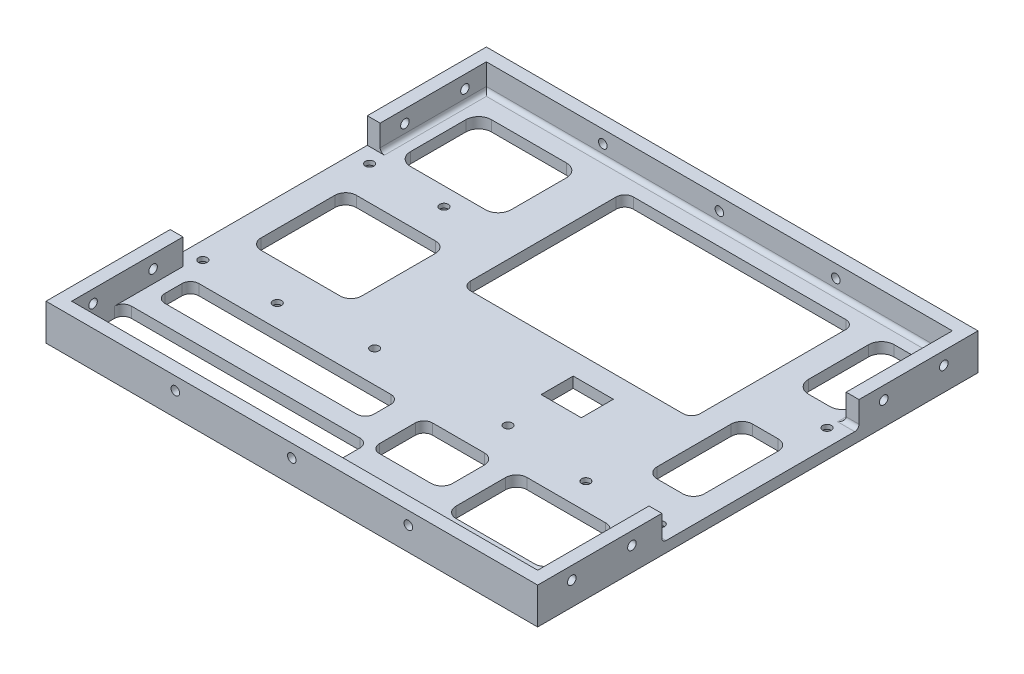
SolidWorks part; units mm, degrees
material "Custom Plastic"
ref_plane "Front Plane" through (0, 0, 0) normal (0, 0, 1) x (1, 0, 0)
ref_plane "Top Plane" through (0, 0, 0) normal (0, 1, 0) x (1, 0, 0)
ref_plane "Right Plane" through (0, 0, 0) normal (1, 0, 0) x (0, 0, -1)
sketch "Sketch1" plane through (0, 0, 0) normal (0, 1, 0) x (1, 0, 0)
  line L1 (-59.5, -51.5) -> (59.5, -51.5)
  line L2 (-59.5, -51.5) -> (-59.5, 51.5)
  line L3 (-59.5, 51.5) -> (59.5, 51.5)
  line L4 (59.5, -51.5) -> (59.5, 51.5)
  line L5 (-59.5, -51.5) -> (59.5, 51.5) construction
  line L6 (-59.5, 51.5) -> (59.5, -51.5) construction
  point P0 (0, 0)
  dimension "D1" = 119
  dimension "D2" = 103
extrude "Boss-Extrude1" add sketch "Sketch1" along normal blind 2.5
sketch "Sketch3" plane through (0, 2.5, 0) normal (0, 1, 0) x (1, 0, 0)
  line L0 (-59.5, -51.5) -> (59.5, -51.5) construction
  line L1 (-18.5, -5.5) -> (36.5, -5.5)
  line L2 (-18.5, -5.5) -> (-18.5, 38.5)
  line L3 (-18.5, 38.5) -> (36.5, 38.5)
  line L4 (36.5, -5.5) -> (36.5, 38.5)
  line L5 (-18.5, -5.5) -> (36.5, 38.5) construction
  line L6 (-18.5, 38.5) -> (36.5, -5.5) construction
  line L7 (-59.5, 51.5) -> (-59.5, -51.5) construction
  point P0 (9, 16.5)
  dimension "D1" = 46
  dimension "D2" = 41
  dimension "D3" = 44
  dimension "D4" = 55
extrude "Cut-Extrude2" cut sketch "Sketch3" against normal blind 10
sketch "Sketch4" plane through (-59.5, 0, 0) normal (-1, 0, 0) x (0, 0, 1)
  line L4 (-51.5, 0) -> (51.5, 0)
  line L5 (51.5, 0) -> (51.5, 2.5)
  line L6 (51.5, 2.5) -> (-51.5, 2.5)
  line L7 (-51.5, 2.5) -> (-51.5, 0)
  line L8 (-51.5, 0) -> (51.5, 0)
  line L9 (51.5, 0) -> (51.5, 2.5)
  line L10 (51.5, 2.5) -> (-51.5, 2.5)
  line L11 (-51.5, 2.5) -> (-51.5, 0)
  dimension "D1" = 0
extrude "Boss-Extrude2" add sketch "Sketch4" along normal blind 1.5
sketch "Sketch5" plane through (59.5, 0, 0) normal (1, 0, 0) x (0, 0, -1)
  line L4 (-51.5, 0) -> (51.5, 0)
  line L5 (51.5, 0) -> (51.5, 2.5)
  line L6 (51.5, 2.5) -> (-51.5, 2.5)
  line L7 (-51.5, 2.5) -> (-51.5, 0)
  line L8 (-51.5, 0) -> (51.5, 0)
  line L9 (51.5, 0) -> (51.5, 2.5)
  line L10 (51.5, 2.5) -> (-51.5, 2.5)
  line L11 (-51.5, 2.5) -> (-51.5, 0)
  dimension "D1" = 0
extrude "Boss-Extrude3" add sketch "Sketch5" along normal blind 1.5
sketch "Sketch6" plane through (-61, 0, 0) normal (-1, 0, 0) x (0, 0, 1)
  line L4 (-51.5, 2.5) -> (-51.5, 0)
  line L5 (-51.5, 0) -> (51.5, 0)
  line L6 (51.5, 0) -> (51.5, 2.5)
  line L7 (51.5, 2.5) -> (-51.5, 2.5)
  line L8 (-51.5, 2.5) -> (-51.5, 0)
  line L9 (-51.5, 0) -> (51.5, 0)
  line L10 (51.5, 0) -> (51.5, 2.5)
  line L11 (51.5, 2.5) -> (-51.5, 2.5)
  dimension "D1" = 0
extrude "Cut-Extrude3" cut sketch "Sketch6" against normal blind 3.5
sketch "Sketch7" plane through (61, 0, 0) normal (1, 0, 0) x (0, 0, -1)
  line L4 (-51.5, 2.5) -> (-51.5, 0)
  line L5 (-51.5, 0) -> (51.5, 0)
  line L6 (51.5, 0) -> (51.5, 2.5)
  line L7 (51.5, 2.5) -> (-51.5, 2.5)
  line L8 (-51.5, 2.5) -> (-51.5, 0)
  line L9 (-51.5, 0) -> (51.5, 0)
  line L10 (51.5, 0) -> (51.5, 2.5)
  line L11 (51.5, 2.5) -> (-51.5, 2.5)
  dimension "D1" = 0
extrude "Cut-Extrude4" cut sketch "Sketch7" against normal blind 3.5
sketch "Sketch8" plane through (0, 2.5, 0) normal (0, 1, 0) x (1, 0, 0)
  line L0 (-57.5, -51.5) -> (-57.5, 51.5) construction
  line L1 (-57.5, -51.5) -> (57.5, -51.5) construction
  line L3 (0, 59.9293) -> (0, -77.2132) construction
  circle A0 centre (-15.5, -44.96) radius 1
  circle A1 centre (15.7, -44.96) radius 1
  circle A2 centre (-15.5, -16.63) radius 1
  circle A3 centre (15.7, -16.63) radius 1
  circle A4 centre (-53.5, -18.81) radius 1
  circle A5 centre (-36.1, -18.81) radius 1
  circle A6 centre (-53.5, 20.19) radius 1
  circle A7 centre (-36.1, 20.19) radius 1
  circle A8 centre (36.1, -18.81) radius 1
  circle A9 centre (53.5, -18.81) radius 1
  circle A10 centre (53.5, 20.19) radius 1
  dimension "D1" = 2
  dimension "D2" = 2
  dimension "D7" = 2
  dimension "D8" = 2
  dimension "D13" = 2
  dimension "D14" = 2
  dimension "D15" = 2
  dimension "D16" = 2
  dimension "D3" = 42
  dimension "D4" = 31.2
  dimension "D5" = 6.54
  dimension "D6" = 6.54
  dimension "D9" = 28.33
  dimension "D10" = 28.33
  dimension "D11" = 32.69
  dimension "D12" = 4
  dimension "D17" = 4
  dimension "D18" = 39
  dimension "D19" = 17.4
extrude "Cut-Extrude5" cut sketch "Sketch8" against normal blind 10
sketch "Sketch12" plane through (0, 2.5, 0) normal (0, 1, 0) x (1, 0, 0)
  line L0 (18.4571, -37.3668) -> (6.3413, -37.3668)
  line L1 (-48.6757, -10.0359) -> (-30.1363, -10.0359)
  line L2 (-51.1757, -7.5359) -> (-51.1757, 9.7595)
  line L3 (-48.6757, 12.2595) -> (-30.1363, 12.2595)
  line L4 (-27.6363, -7.5359) -> (-27.6363, 9.7595)
  line L5 (-51.1757, -10.0359) -> (-27.6363, 12.2595) construction
  line L6 (-51.1757, 12.2595) -> (-27.6363, -10.0359) construction
  line L7 (4.3413, -35.3668) -> (4.3413, -26.9455)
  line L8 (6.3413, -24.9455) -> (18.4571, -24.9455)
  line L9 (-57.5, -51.5) -> (57.5, -51.5) construction
  line L10 (0.9414, -48.5) -> (-52.5, -48.5)
  line L11 (2.9414, -46.5) -> (2.9414, -38.5)
  line L12 (20.9571, -34.8668) -> (20.9571, -27.4455)
  line L13 (0.9414, -36.5) -> (-52.5, -36.5)
  line L14 (28.4571, -41.5653) -> (46.8503, -41.5653)
  line L15 (49.3503, -39.0653) -> (49.3503, -27.4455)
  line L16 (46.8503, -24.9455) -> (28.4571, -24.9455)
  line L17 (25.9571, -27.4455) -> (25.9571, -39.0653)
  line L18 (0, 20.449) -> (0, -71.2445) construction
  line L19 (41.5, 9.7595) -> (41.5, -7.5359)
  line L20 (44, -10.0359) -> (50, -10.0359)
  line L21 (52.5, -7.5359) -> (52.5, 9.7595)
  line L22 (50, 12.2595) -> (44, 12.2595)
  line L23 (57.5, 51.5) -> (57.5, -51.5) construction
  line L24 (36.5, -5.5) -> (36.5, 38.5) construction
  line L25 (-54.5, -46.5) -> (-54.5, -38.5)
  line L26 (-57.5, -51.5) -> (-57.5, 51.5) construction
  line L28 (-4.2775, -32.0334) -> (-49.1757, -32.0334)
  line L29 (-2.2775, -30.0334) -> (-2.2775, -26.0334)
  line L30 (-4.2775, -24.0334) -> (-49.1757, -24.0334)
  line L31 (-51.1757, -30.0334) -> (-51.1757, -26.0334)
  line L32 (-30.6363, 24.426) -> (-48.1757, 24.426)
  line L33 (-27.6363, 27.426) -> (-27.6363, 40.3779)
  line L34 (-30.6363, 43.3779) -> (-48.1757, 43.3779)
  line L35 (-51.1757, 27.426) -> (-51.1757, 40.3779)
  line L36 (49.5, 24.8453) -> (44.5, 24.8453)
  line L37 (52.5, 27.8453) -> (52.5, 41.8947)
  line L38 (49.5, 44.8947) -> (44.5, 44.8947)
  line L39 (41.5, 27.8453) -> (41.5, 41.8947)
  arc A0 (52.5, 9.7595) -> (50, 12.2595) centre (50, 9.7595) ccw
  arc A1 (50, -10.0359) -> (52.5, -7.5359) centre (50, -7.5359) ccw
  arc A2 (41.5, -7.5359) -> (44, -10.0359) centre (44, -7.5359) ccw
  arc A3 (41.5, 9.7595) -> (44, 12.2595) centre (44, 9.7595) cw
  arc A4 (49.3503, -27.4455) -> (46.8503, -24.9455) centre (46.8503, -27.4455) ccw
  arc A5 (46.8503, -41.5653) -> (49.3503, -39.0653) centre (46.8503, -39.0653) ccw
  arc A6 (28.4571, -41.5653) -> (25.9571, -39.0653) centre (28.4571, -39.0653) cw
  arc A7 (28.4571, -24.9455) -> (25.9571, -27.4455) centre (28.4571, -27.4455) ccw
  arc A8 (20.9571, -27.4455) -> (18.4571, -24.9455) centre (18.4571, -27.4455) ccw
  arc A9 (18.4571, -37.3668) -> (20.9571, -34.8668) centre (18.4571, -34.8668) ccw
  arc A10 (6.3413, -24.9455) -> (4.3413, -26.9455) centre (6.3413, -26.9455) ccw
  arc A11 (6.3413, -37.3668) -> (4.3413, -35.3668) centre (6.3413, -35.3668) cw
  arc A12 (0.9414, -48.5) -> (2.9414, -46.5) centre (0.9414, -46.5) ccw
  arc A13 (2.9414, -38.5) -> (0.9414, -36.5) centre (0.9414, -38.5) ccw
  arc A14 (-52.5, -36.5) -> (-54.5, -38.5) centre (-52.5, -38.5) ccw
  arc A15 (-52.5, -48.5) -> (-54.5, -46.5) centre (-52.5, -46.5) cw
  arc A16 (-30.1363, 12.2595) -> (-27.6363, 9.7595) centre (-30.1363, 9.7595) cw
  arc A17 (-30.1363, -10.0359) -> (-27.6363, -7.5359) centre (-30.1363, -7.5359) ccw
  arc A18 (-48.6757, -10.0359) -> (-51.1757, -7.5359) centre (-48.6757, -7.5359) cw
  arc A19 (-51.1757, 9.7595) -> (-48.6757, 12.2595) centre (-48.6757, 9.7595) cw
  arc A20 (-49.1757, -32.0334) -> (-51.1757, -30.0334) centre (-49.1757, -30.0334) cw
  arc A21 (-49.1757, -24.0334) -> (-51.1757, -26.0334) centre (-49.1757, -26.0334) ccw
  arc A22 (-2.2775, -26.0334) -> (-4.2775, -24.0334) centre (-4.2775, -26.0334) ccw
  arc A23 (-4.2775, -32.0334) -> (-2.2775, -30.0334) centre (-4.2775, -30.0334) ccw
  arc A24 (-27.6363, 40.3779) -> (-30.6363, 43.3779) centre (-30.6363, 40.3779) ccw
  arc A25 (-48.1757, 43.3779) -> (-51.1757, 40.3779) centre (-48.1757, 40.3779) ccw
  arc A26 (-48.1757, 24.426) -> (-51.1757, 27.426) centre (-48.1757, 27.426) cw
  arc A27 (-30.6363, 24.426) -> (-27.6363, 27.426) centre (-30.6363, 27.426) ccw
  arc A28 (52.5, 41.8947) -> (49.5, 44.8947) centre (49.5, 41.8947) ccw
  arc A29 (44.5, 44.8947) -> (41.5, 41.8947) centre (44.5, 41.8947) ccw
  arc A30 (44.5, 24.8453) -> (41.5, 27.8453) centre (44.5, 27.8453) cw
  arc A31 (49.5, 24.8453) -> (52.5, 27.8453) centre (49.5, 27.8453) ccw
  point P0 (-39.406, 1.1118)
  point P10 (0, -37.3668)
  point P23 (52.5, 1.1118)
  point P51 (0, -24.9455)
  dimension "D5" = 2.5
  dimension "D1" = 2
  dimension "D9" = 2
  dimension "D10" = 2
  dimension "D11" = 2
  dimension "D13" = 3
  dimension "D14" = 3
  dimension "D2" = 5
  dimension "D3" = 5
  dimension "D4" = 5
  dimension "D6" = 3
  dimension "D7" = 3
  dimension "D8" = 12
  dimension "D12" = 8
extrude "Cut-Extrude9" cut sketch "Sketch12" against normal blind 11
sketch "Sketch13" plane through (0, 2.5, 0) normal (0, 1, 0) x (1, 0, 0)
  line L0 (21.7127, -5.5) -> (36.5, -5.5)
  line L1 (-18.5, -5.5) -> (36.5, -5.5) construction
  line L2 (36.5, -5.5) -> (36.5, 7.734)
  line L3 (36.5, -5.5) -> (36.5, 38.5) construction
  line L4 (34.2775, 7.734) -> (26.8569, 7.734)
  line L5 (26.8569, 7.734) -> (26.8569, 35.8003)
  line L6 (36.5, 38.5) -> (-18.5, 38.5) construction
  line L7 (-8.4281, 38.5) -> (26.4281, 38.5)
  line L8 (9, 38.5) -> (9, -5.5) construction
  line L9 (3.6846, -5.5) -> (14.3154, -5.5)
  line L10 (14.3154, -5.5) -> (14.3154, -0.0636)
  line L11 (14.3154, -0.0636) -> (21.7127, -0.0636)
  line L12 (21.7127, -0.0636) -> (21.7127, -5.5)
  line L13 (34.2775, 7.734) -> (34.2775, 35.8003)
  line L14 (36.5, 7.734) -> (36.5, 38.5)
  line L15 (36.5, 38.5) -> (33.8487, 38.5)
  line L16 (3.6846, -5.5) -> (-3.7127, -5.5)
  line L19 (-3.7127, -5.5) -> (-18.5, -5.5)
  line L20 (-18.5, -5.5) -> (-18.5, 7.734)
  line L21 (-18.5, 7.734) -> (-18.5, 38.5)
  line L22 (-8.8569, 7.734) -> (-8.8569, 35.8432)
  line L23 (-16.2775, 7.734) -> (-8.8569, 7.734)
  line L24 (-16.2775, 7.734) -> (-16.2775, 35.8432)
  line L25 (26.8569, 35.8003) -> (34.2775, 35.8003)
  line L26 (-8.8569, 35.8432) -> (-16.2775, 35.8432)
  line L27 (-18.5, 38.5) -> (-8.4281, 38.5)
  line L28 (36.5, 38.5) -> (26.4281, 38.5)
  point P27 (-15.8487, 38.5)
extrude "Boss-Extrude4" add sketch "Sketch13" against normal up to surface (2.5 mm away)
sketch "Sketch14" plane through (0, 2.5, 0) normal (0, 1, 0) x (1, 0, 0)
  line L0 (57.5, 23.6591) -> (54.5, 23.6591)
  line L1 (57.5, 51.5) -> (57.5, -51.5) construction
  line L2 (54.5, 23.6591) -> (54.5, 48.5)
  line L3 (54.5, 48.5) -> (-54.5, 48.5)
  line L4 (-54.5, 48.5) -> (-54.5, 23.6591)
  line L5 (-54.5, 23.6591) -> (-57.5, 23.6591)
  line L6 (-57.5, -51.5) -> (-57.5, 51.5) construction
  line L7 (-57.5, 23.6591) -> (-57.5, 51.5)
  line L8 (-57.5, 51.5) -> (57.5, 51.5)
  line L9 (57.5, 51.5) -> (57.5, 23.6591)
  line L10 (57.5, -22.4516) -> (54.5, -22.4516)
  line L11 (54.5, -22.4516) -> (54.5, -48.5)
  line L12 (54.5, -48.5) -> (-54.5, -48.5)
  line L13 (-54.5, -48.5) -> (-54.5, -22.4516)
  line L14 (-54.5, -22.4516) -> (-57.5, -22.4516)
  line L15 (-57.5, -22.4516) -> (-57.5, -51.5)
  line L16 (-57.5, -51.5) -> (57.5, -51.5)
  line L17 (57.5, -51.5) -> (57.5, -22.4516)
  dimension "D1" = 3
  dimension "D2" = 3
  dimension "D3" = 3
  dimension "D4" = 3
  dimension "D5" = 3
  dimension "D6" = 3
extrude "Boss-Extrude5" add sketch "Sketch14" along normal blind 5
fillet "Fillet1" radius 1 6 edges at (-54.5, 2.5, -36.0795) (0, 2.5, -48.5) (54.5, 2.5, -36.0795) (56, 2.5, 22.4516) (54.5, 2.5, 35.4758) (-54.5, 2.5, 47.5)
sketch "Sketch15" plane through (54.5, 0, 0) normal (-1, 0, 0) x (0, 0, 1)
  line L0 (22.4516, 7.5) -> (48.5, 7.5) construction
  line L1 (22.4516, 7.5) -> (22.4516, 3.5) construction
  line L2 (48.5, 7.5) -> (48.5, 3.5) construction
  circle A0 centre (29.4516, 5.5) radius 1
  circle A1 centre (43.5, 5.5) radius 1
  point P10 (48.5, 5.5)
  dimension "D1" = 2
  dimension "D4" = 2
  dimension "D2" = 2
  dimension "D3" = 7
  dimension "D5" = 5
extrude "Cut-Extrude10" cut sketch "Sketch15" against normal blind 5
sketch "Sketch16" plane through (0, 0, 48.5) normal (0, 0, -1) x (-1, 0, 0)
  line L0 (-54.5, 7.5) -> (54.5, 7.5) construction
  circle A0 centre (0, 5.5) radius 1
  circle A1 centre (-27.25, 5.5) radius 1
  circle A2 centre (27.25, 5.5) radius 1
  dimension "D1" = 2
  dimension "D2" = 2
  dimension "D3" = 2
  dimension "D5" = 2
  dimension "D4" = 27.25
  dimension "D6" = 27.25
extrude "Cut-Extrude11" cut sketch "Sketch16" against normal blind 5
sketch "Sketch17" plane through (0, 7.5, 0) normal (0, 1, 0) x (1, 0, 0)
  line L8 (57.5, -51.5) -> (57.5, -22.4516)
  line L9 (57.5, -22.4516) -> (54.5, -22.4516)
  line L10 (54.5, -22.4516) -> (54.5, -48.5)
  line L11 (54.5, -48.5) -> (-54.5, -48.5)
  line L12 (-54.5, -48.5) -> (-54.5, -22.4516)
  line L13 (-54.5, -22.4516) -> (-57.5, -22.4516)
  line L14 (-57.5, -22.4516) -> (-57.5, -51.5)
  line L15 (-57.5, -51.5) -> (57.5, -51.5)
  line L16 (57.5, -51.5) -> (57.5, -22.4516)
  line L17 (57.5, -22.4516) -> (54.5, -22.4516)
  line L18 (54.5, -22.4516) -> (54.5, -48.5)
  line L19 (54.5, -48.5) -> (-54.5, -48.5)
  line L20 (-54.5, -48.5) -> (-54.5, -22.4516)
  line L21 (-54.5, -22.4516) -> (-57.5, -22.4516)
  line L22 (-57.5, -22.4516) -> (-57.5, -51.5)
  line L23 (-57.5, -51.5) -> (57.5, -51.5)
  line L24 (57.5, 23.6591) -> (57.5, 51.5)
  line L25 (57.5, 51.5) -> (-57.5, 51.5)
  line L26 (-57.5, 51.5) -> (-57.5, 23.6591)
  line L27 (-57.5, 23.6591) -> (-54.5, 23.6591)
  line L28 (-54.5, 23.6591) -> (-54.5, 48.5)
  line L29 (-54.5, 48.5) -> (54.5, 48.5)
  line L30 (54.5, 48.5) -> (54.5, 23.6591)
  line L31 (54.5, 23.6591) -> (57.5, 23.6591)
  line L32 (57.5, 23.6591) -> (57.5, 51.5)
  line L33 (57.5, 51.5) -> (-57.5, 51.5)
  line L34 (-57.5, 51.5) -> (-57.5, 23.6591)
  line L35 (-57.5, 23.6591) -> (-54.5, 23.6591)
  line L36 (-54.5, 23.6591) -> (-54.5, 48.5)
  line L37 (-54.5, 48.5) -> (54.5, 48.5)
  line L38 (54.5, 48.5) -> (54.5, 23.6591)
  line L39 (54.5, 23.6591) -> (57.5, 23.6591)
  dimension "D1" = 0
  dimension "D2" = 0
extrude "Boss-Extrude6" add sketch "Sketch17" along normal blind 1
ref_plane "Plane1" through (0, 0, 0) normal (0, 0, 1) x (1, 0, 0)
mirror "Mirror1" about plane through (0, 0, 0) normal (0, 0, 1) of "Cut-Extrude10", "Cut-Extrude11"
ref_plane "Plane2" through (0, 0, 0) normal (1, 0, 0) x (0, 0, -1)
mirror "Mirror2" about plane through (0, 0, 0) normal (1, 0, 0) of "Cut-Extrude10"
sketch "Sketch18" plane through (-54.5, 0, 0) normal (1, 0, 0) x (0, 0, -1)
  circle A0 centre (43.5, 5.5) radius 1 construction
  circle A1 centre (29.4516, 5.5) radius 1 construction
  circle A2 centre (43.5, 5.5) radius 1
  circle A3 centre (29.4516, 5.5) radius 1
extrude "Cut-Extrude12" cut sketch "Sketch18" against normal blind 10
sketch "Sketch19" plane through (0, 2.5, 0) normal (0, 1, 0) x (1, 0, 0)
  line L0 (26.8569, 7.734) -> (26.8569, 35.8003) construction
  line L1 (35.7775, 37.3003) -> (25.3569, 37.3003)
  line L2 (35.7775, 37.3003) -> (35.7775, 6.234)
  line L3 (35.7775, 6.234) -> (25.3569, 6.234)
  line L4 (25.3569, 37.3003) -> (25.3569, 6.234)
  line L5 (35.7775, 37.3003) -> (25.3569, 6.234) construction
  line L6 (35.7775, 6.234) -> (25.3569, 37.3003) construction
  line L7 (34.2775, 7.734) -> (26.8569, 7.734) construction
  line L8 (34.2775, 7.734) -> (34.2775, 35.8003) construction
  line L9 (26.8569, 35.8003) -> (34.2775, 35.8003) construction
  line L10 (-16.2775, 7.734) -> (-16.2775, 35.8432) construction
  line L11 (-7.3569, 37.3432) -> (-17.7775, 37.3432)
  line L12 (-7.3569, 37.3432) -> (-7.3569, 6.234)
  line L13 (-7.3569, 6.234) -> (-17.7775, 6.234)
  line L14 (-17.7775, 37.3432) -> (-17.7775, 6.234)
  line L15 (-7.3569, 37.3432) -> (-17.7775, 6.234) construction
  line L16 (-7.3569, 6.234) -> (-17.7775, 37.3432) construction
  line L17 (-16.2775, 7.734) -> (-8.8569, 7.734) construction
  line L18 (-8.8569, 7.734) -> (-8.8569, 35.8432) construction
  line L19 (-8.8569, 35.8432) -> (-16.2775, 35.8432) construction
  line L20 (14.3154, -5.5) -> (21.7127, -5.5) construction
  line L21 (22.7127, 1) -> (13.3154, 1)
  line L22 (22.7127, 1) -> (22.7127, -6.5)
  line L23 (22.7127, -6.5) -> (13.3154, -6.5)
  line L24 (13.3154, 1) -> (13.3154, -6.5)
  line L25 (22.7127, 1) -> (13.3154, -6.5) construction
  line L26 (22.7127, -6.5) -> (13.3154, 1) construction
  line L27 (14.3154, -5.5) -> (14.3154, -0.0636) construction
  line L28 (-4.675, 0) -> (4.675, 0) construction
  line L29 (21.7127, -0.0636) -> (21.7127, -5.5) construction
  point P0 (30.5672, 21.7672)
  point P7 (30.5672, 6.234)
  point P14 (-12.5672, 21.7886)
  point P27 (18.0141, -2.75)
  dimension "D1" = 1.5
  dimension "D2" = 1.5
  dimension "D3" = 1.5
  dimension "D4" = 1.5
  dimension "D5" = 1.5
  dimension "D6" = 1.5
  dimension "D7" = 1.5
  dimension "D8" = 1.5
  dimension "D9" = 1
  dimension "D10" = 1
  dimension "D11" = 1
  dimension "D12" = 1
extrude "Cut-Extrude13" cut sketch "Sketch19" against normal blind 10
sketch "Sketch20" plane through (0, 0, 0) normal (0, -1, 0) x (1, 0, 0)
  circle A0 centre (-53.5, 18.81) radius 2
  circle A1 centre (-36.1, 18.81) radius 2
  circle A2 centre (-53.5, -20.19) radius 2
  circle A3 centre (-36.1, -20.19) radius 2
  circle A4 centre (53.5, 18.81) radius 2
  circle A5 centre (36.1, 18.81) radius 2
  circle A6 centre (53.5, -20.19) radius 2
  dimension "D1" = 4
  dimension "D2" = 4
  dimension "D3" = 4
  dimension "D4" = 4
  dimension "D5" = 4
  dimension "D6" = 4
  dimension "D7" = 4
extrude "Cut-Extrude14" cut sketch "Sketch20" against normal blind 1.5
sketch "Sketch21" plane through (0, 2.5, 0) normal (0, 1, 0) x (1, 0, 0)
  line L1 (35.7775, 6.234) -> (-17.9477, 6.234)
  line L2 (35.7775, 6.234) -> (35.7775, 44.3217)
  line L3 (35.7775, 44.3217) -> (-17.9477, 44.3217)
  line L4 (-17.9477, 6.234) -> (-17.9477, 44.3217)
extrude "Cut-Extrude15" cut sketch "Sketch21" against normal blind 21.5
fillet "Fillet2" radius 2 4 edges at (-17.9477, 1.25, -44.3217) (35.7775, 1.25, -44.3217) (35.7775, 1.25, -6.234) (-17.9477, 1.25, -6.234)
